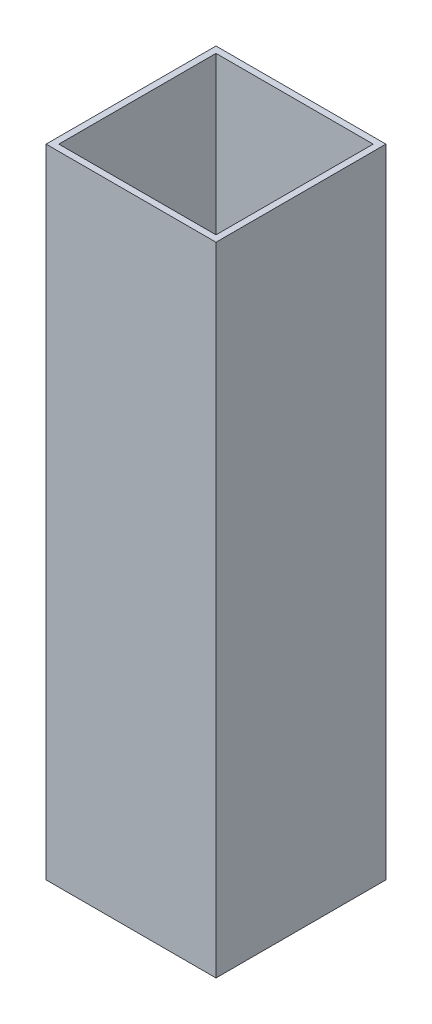
SolidWorks part; units mm, degrees
material "AISI 1020"
ref_plane "Plano frontal" through (0, 0, 0) normal (0, 0, 1) x (1, 0, 0)
ref_plane "Plano superior" through (0, 0, 0) normal (0, 1, 0) x (1, 0, 0)
ref_plane "Plano direito" through (0, 0, 0) normal (1, 0, 0) x (0, 0, -1)
sketch "Esboço1" plane through (0, 0, 0) normal (0, 1, 0) x (1, 0, 0)
  line L1 (-20, -20) -> (20, -20)
  line L2 (-20, -20) -> (-20, 20)
  line L3 (-20, 20) -> (20, 20)
  line L4 (20, -20) -> (20, 20)
  line L5 (-20, -20) -> (20, 20) construction
  line L6 (-20, 20) -> (20, -20) construction
  point P0 (0, 0)
  dimension "D1" = 40
  dimension "D2" = 40
extrude "Ressalto-extrusão1" add sketch "Esboço1" along normal blind 150
sketch "Esboço2" plane through (0, 0, 0) normal (0, -1, 0) x (1, 0, 0)
  line L1 (-18.5, -18.5) -> (18.5, -18.5)
  line L2 (-18.5, -18.5) -> (-18.5, 18.5)
  line L3 (-18.5, 18.5) -> (18.5, 18.5)
  line L4 (18.5, -18.5) -> (18.5, 18.5)
  line L5 (-18.5, -18.5) -> (18.5, 18.5) construction
  line L6 (-18.5, 18.5) -> (18.5, -18.5) construction
  point P0 (0, 0)
  dimension "D1" = 37
  dimension "D2" = 37
extrude "Corte-extrusão1" cut sketch "Esboço2" against normal through all
